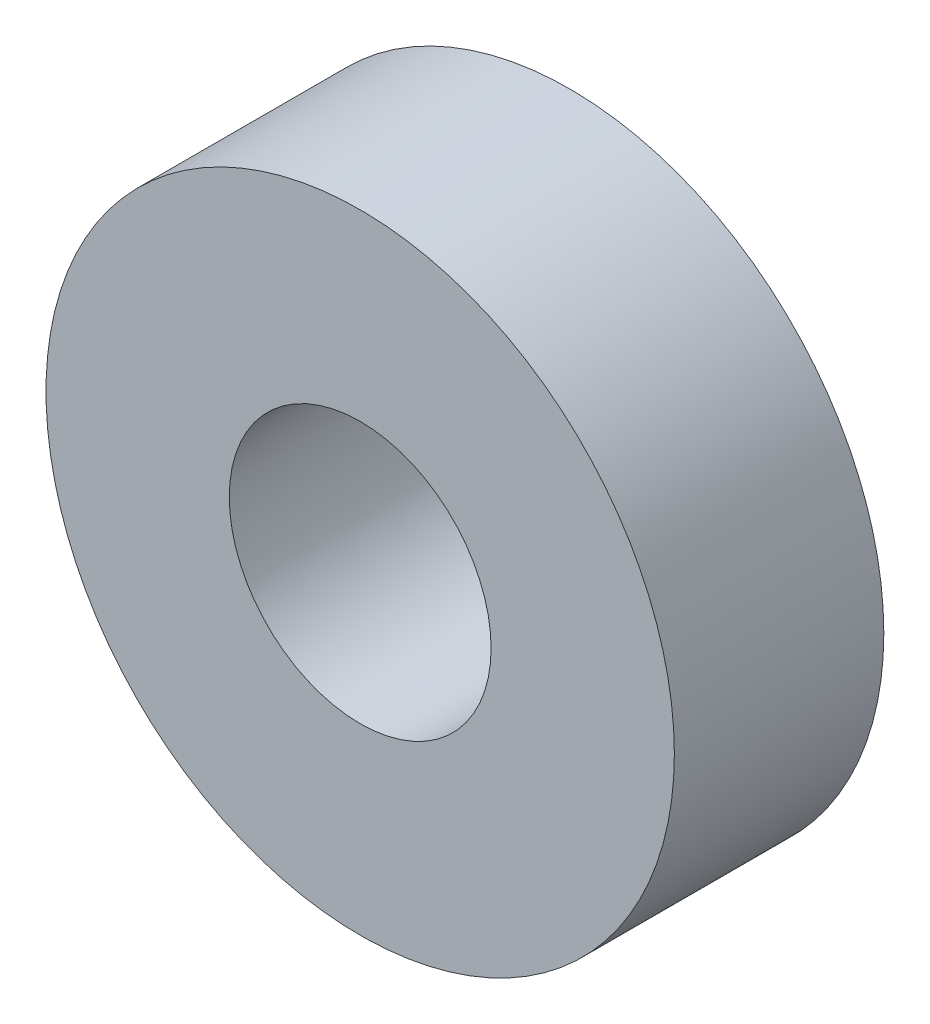
SolidWorks part; units mm, degrees
ref_plane "Plano frontal" through (0, 0, 0) normal (0, 0, 1) x (1, 0, 0)
ref_plane "Plano superior" through (0, 0, 0) normal (0, 1, 0) x (1, 0, 0)
ref_plane "Plano direito" through (0, 0, 0) normal (1, 0, 0) x (0, 0, -1)
sketch "Esboço1" plane through (0, 0, 0) normal (0, 0, 1) x (1, 0, 0)
  circle A0 centre (0, 0) radius 6
  circle A1 centre (0, 0) radius 2.5
  dimension "D1" = 5
  dimension "D2" = 12
extrude "Ressalto-extrusão1" add sketch "Esboço1" along normal blind 4
